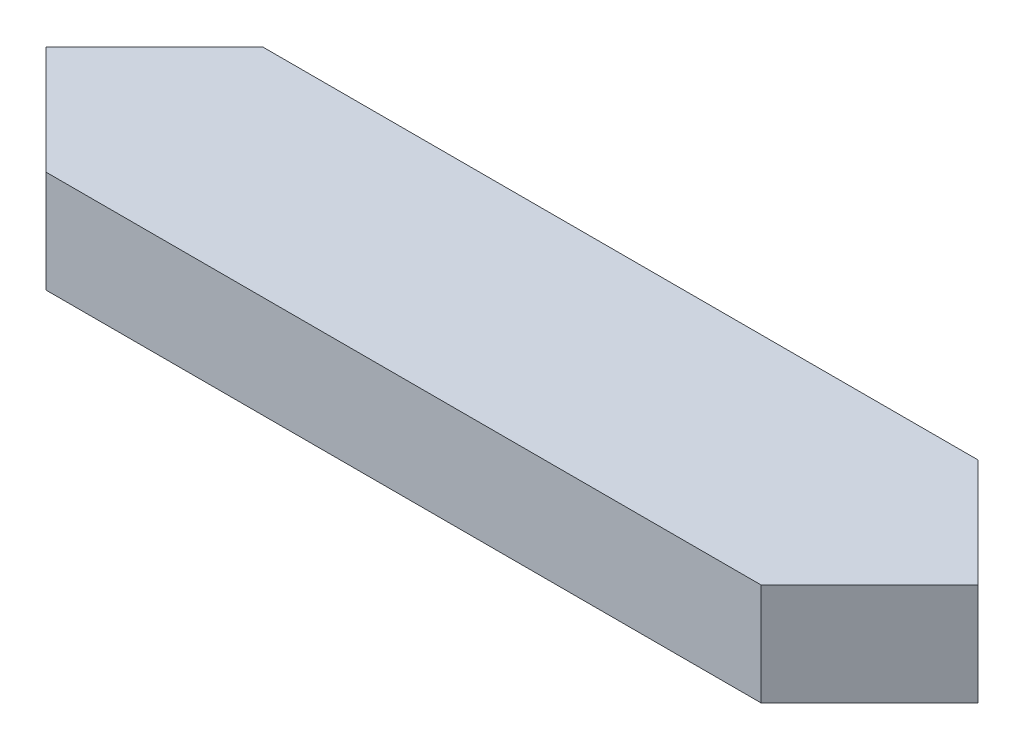
SolidWorks part; units mm, degrees
material "ABS"
ref_plane "Front Plane" through (0, 0, 0) normal (0, 0, 1) x (1, 0, 0)
ref_plane "Top Plane" through (0, 0, 0) normal (0, 1, 0) x (1, 0, 0)
ref_plane "Right Plane" through (0, 0, 0) normal (1, 0, 0) x (0, 0, -1)
sketch "Sketch1" plane through (0, 0, 0) normal (0, 1, 0) x (1, 0, 0)
  line L0 (0, 0) -> (2.8315, 0) construction
  line L1 (0, 0) -> (0.2694, 0.2694)
  line L2 (0.2694, 0.2694) -> (2.0474, 0.2694)
  line L3 (2.0474, 0.2694) -> (2.3168, 0)
  line L4 (2.0474, -0.2694) -> (2.3168, 0)
  line L5 (0, 0) -> (0.2694, -0.2694)
  line L6 (0.2694, -0.2694) -> (2.0474, -0.2694)
  dimension "D1" = 1.778
  dimension "D2" = 0.381
extrude "Boss-Extrude1" add sketch "Sketch1" along normal blind 0.254
